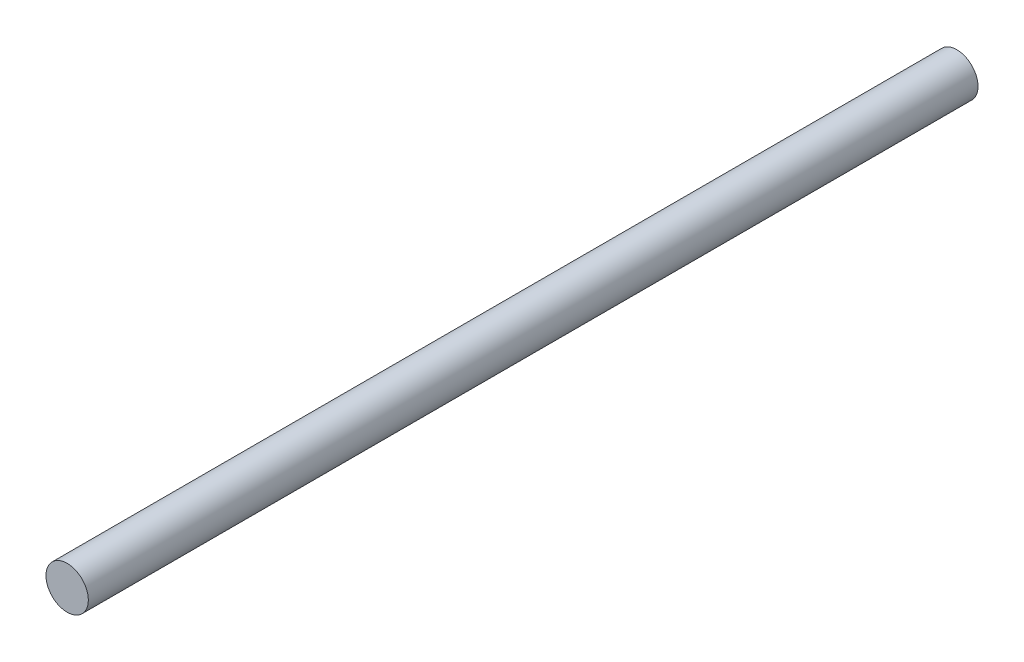
SolidWorks part; units mm, degrees
ref_plane "Front Plane" through (0, 0, 0) normal (0, 0, 1) x (1, 0, 0)
ref_plane "Top Plane" through (0, 0, 0) normal (0, 1, 0) x (1, 0, 0)
ref_plane "Right Plane" through (0, 0, 0) normal (1, 0, 0) x (0, 0, -1)
sketch "Sketch1" plane through (0, 0, 0) normal (0, 0, 1) x (1, 0, 0)
  circle A0 centre (0, 0) radius 0.5
  dimension "D1" = 1
extrude "Boss-Extrude1" add sketch "Sketch1" along normal blind 21
